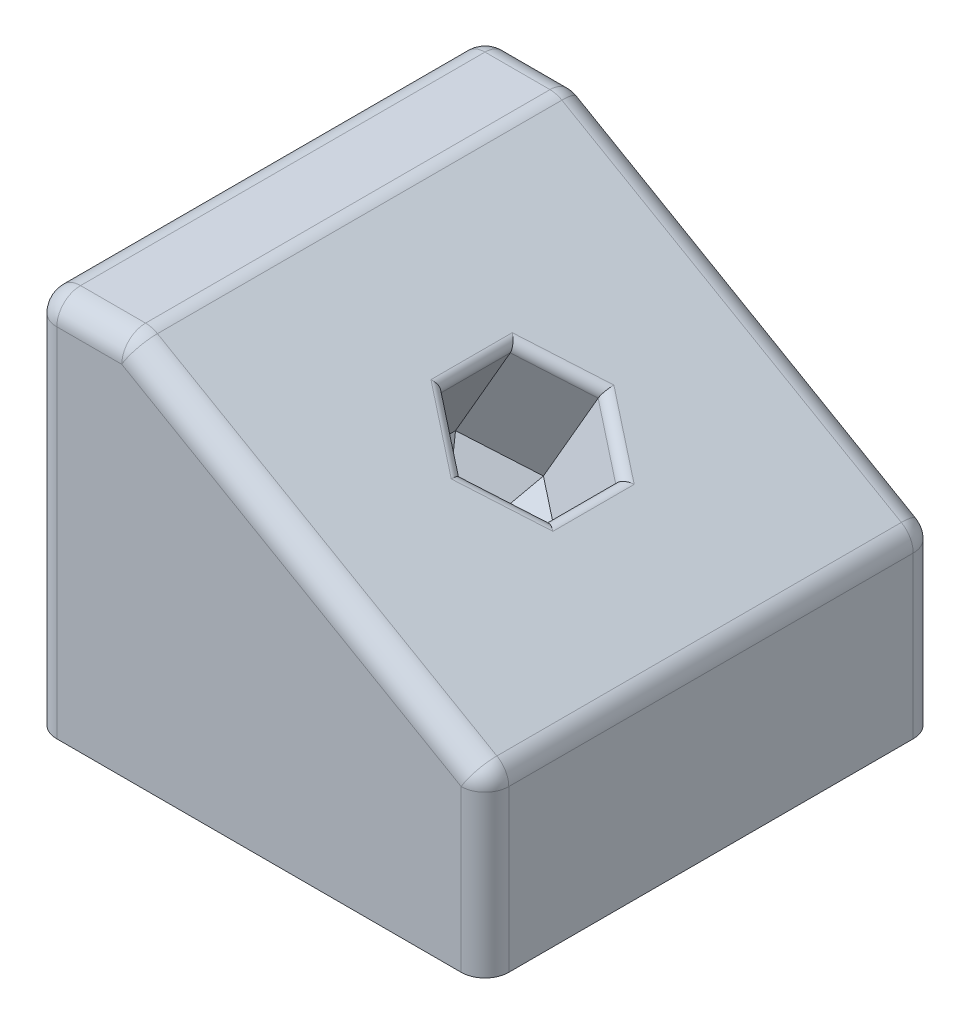
SolidWorks part; units mm, degrees
ref_plane "Front Plane" through (0, 0, 0) normal (0, 0, 1) x (1, 0, 0)
ref_plane "Top Plane" through (0, 0, 0) normal (0, 1, 0) x (1, 0, 0)
ref_plane "Right Plane" through (0, 0, 0) normal (1, 0, 0) x (0, 0, -1)
sketch "Sketch1" plane through (0, 0, 0) normal (0, 1, 0) x (1, 0, 0)
  line L1 (-23.8513, -26.2632) -> (96.7987, -26.2632)
  line L2 (-23.8513, -26.2632) -> (-23.8513, 94.3868)
  line L3 (-23.8513, 94.3868) -> (96.7987, 94.3868)
  line L4 (96.7987, -26.2632) -> (96.7987, 94.3868)
  dimension "D1" = 120.65
  dimension "D2" = 120.65
extrude "Boss-Extrude1" add sketch "Sketch1" along normal blind 101.6
sketch "Sketch3" plane through (0, 0, 26.2632) normal (0, 0, 1) x (1, 0, 0)
  line L0 (96.7987, 101.6) -> (1.5487, 101.6)
  line L1 (-23.8513, 101.6) -> (96.7987, 101.6) construction
  line L2 (1.5487, 101.6) -> (96.7987, 46.6074)
  line L3 (96.7987, 101.6) -> (96.7987, 0) construction
  line L4 (96.7987, 46.6074) -> (96.7987, 101.6)
  dimension "D1" = 30
  dimension "D2" = 95.25
extrude "Cut-Extrude1" cut sketch "Sketch3" against normal blind 120.65
sketch "Sketch4" plane through (44.3813, 76.8706, 0) normal (0.5, 0.866, 0) x (0.866, -0.5, 0)
  line L5 (5.5338, 52.8326) -> (-10.7222, 43.4472)
  line L6 (-10.7222, 43.4472) -> (-10.7222, 24.6764)
  line L7 (-10.7222, 24.6764) -> (5.5338, 15.291)
  line L8 (5.5338, 15.291) -> (21.7898, 24.6764)
  line L9 (21.7898, 24.6764) -> (21.7898, 43.4472)
  line L10 (21.7898, 43.4472) -> (5.5338, 52.8326)
  circle A0 centre (5.5338, 34.0618) radius 18.7708 construction
  point P7 (21.7898, 34.0618)
  dimension "D1" = 32.512
extrude "Cut-Extrude2" cut sketch "Sketch4" against normal blind 31.75
sketch "Sketch5" plane through (28.5063, 49.3743, 0) normal (0.5, 0.866, 0) x (0.866, -0.5, 0)
  line L0 (5.5338, 15.291) -> (21.7898, 24.6764) construction
  line L1 (-10.7222, 24.6764) -> (5.5338, 15.291) construction
  line L2 (-10.7222, 43.4472) -> (-10.7222, 24.6764) construction
  line L3 (5.5338, 52.8326) -> (-10.7222, 43.4472) construction
  line L4 (21.7898, 43.4472) -> (5.5338, 52.8326) construction
  line L5 (5.5338, 15.291) -> (21.7898, 24.6764)
  line L6 (-10.7222, 24.6764) -> (5.5338, 15.291)
  line L7 (-10.7222, 43.4472) -> (-10.7222, 24.6764)
  line L8 (5.5338, 52.8326) -> (-10.7222, 43.4472)
  line L9 (21.7898, 43.4472) -> (5.5338, 52.8326)
  line L10 (21.7898, 24.6764) -> (21.7898, 43.4472) construction
  line L11 (21.7898, 24.6764) -> (21.7898, 43.4472)
extrude "Cut-Extrude3" cut sketch "Sketch5" against normal blind 6.35 draft 45
fillet "Fillet1" radius 6.35 11 edges at (1.5487, 101.6, -34.0618) (49.1737, 74.1037, -94.3868) (96.7987, 46.6074, -34.0618) (49.1737, 74.1037, 26.2632) (-11.1513, 101.6, -94.3868) (-11.1513, 101.6, 26.2632) (-23.8513, 101.6, -34.0618) (96.7987, 23.3037, 26.2632) (-23.8513, 50.8, 26.2632) (-23.8513, 50.8, -94.3868) (96.7987, 23.3037, -94.3868)
fillet "Fillet2" radius 2.54 6 edges at (56.2128, 70.0397, -19.9837) (63.2518, 65.9757, -34.0618) (56.2128, 70.0397, -48.1399) (42.1347, 78.1677, -48.1399) (35.0956, 82.2317, -34.0618) (42.1347, 78.1677, -19.9837)
